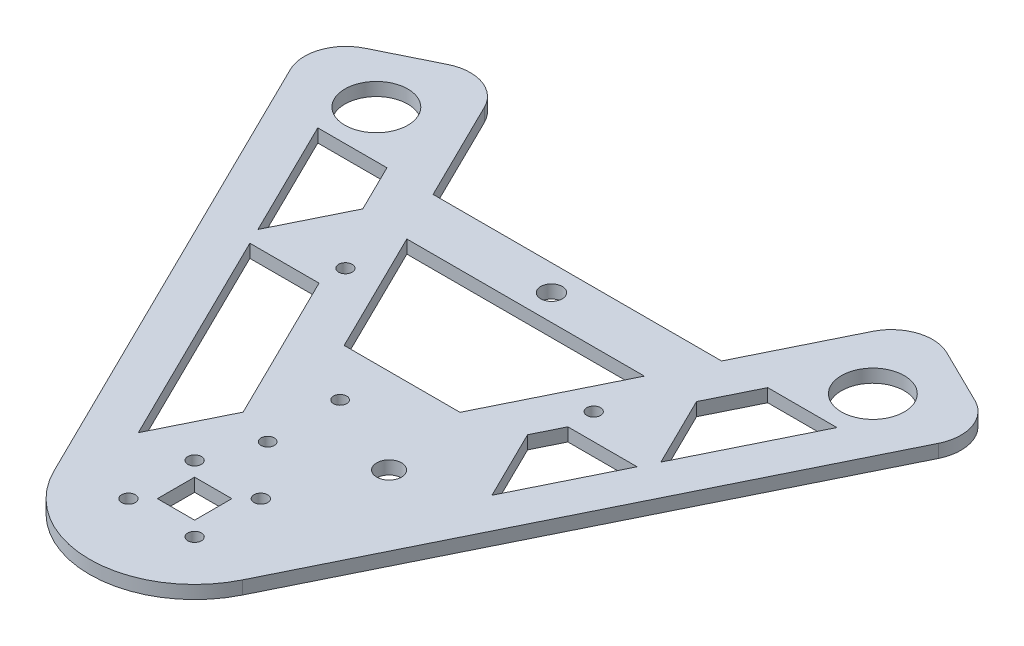
SolidWorks part; units mm, degrees
ref_plane "Front Plane" through (0, 0, 0) normal (0, 0, 1) x (1, 0, 0)
ref_plane "Top Plane" through (0, 0, 0) normal (0, 1, 0) x (1, 0, 0)
ref_plane "Right Plane" through (0, 0, 0) normal (1, 0, 0) x (0, 0, -1)
sketch "Sketch1" plane through (0, 0, 0) normal (0, 1, 0) x (1, 0, 0)
  line L0 (-60, 103.923) -> (60, 103.923) construction
  line L1 (-4.5, -4.5) -> (4.5, -4.5)
  line L2 (-4.5, -4.5) -> (-4.5, 4.5)
  line L3 (-4.5, 4.5) -> (4.5, 4.5)
  line L4 (4.5, -4.5) -> (4.5, 4.5)
  line L5 (-4.5, -4.5) -> (4.5, 4.5) construction
  line L6 (-4.5, 4.5) -> (4.5, -4.5) construction
  line L7 (-82.7138, 110.4306) -> (-22.7854, -11.2243)
  line L8 (22.7854, -11.2243) -> (82.7138, 110.4306)
  line L9 (-51.3166, 125.8972) -> (0, 21.7243)
  line L10 (0, 21.7243) -> (51.3166, 125.8972)
  line L11 (51.3166, 125.8972) -> (82.7138, 110.4306)
  line L12 (-82.7138, 110.4306) -> (-51.3166, 125.8972)
  line L13 (-57.6253, 99.1025) -> (-36.2274, 55.6644) construction
  line L14 (-10.5551, -39.3043) -> (22084.5437, 44813.8629) construction
  line L15 (-14, 50.1443) -> (14, 50.1443)
  line L16 (17.5, 29.5105) -> (-3.1, 29.5105) construction
  line L17 (-8, -8) -> (8, -8) construction
  line L18 (-8, -8) -> (-8, 8) construction
  line L19 (-8, 8) -> (8, 8) construction
  line L20 (8, -8) -> (8, 8) construction
  line L21 (-8, -8) -> (8, 8) construction
  line L22 (-8, 8) -> (8, -8) construction
  line L23 (-3.1, 38.2605) -> (-3.1, 20.7605) construction
  line L24 (-30, 66.4531) -> (30, 66.4531) construction
  line L25 (-34.8648, 92.5) -> (34.8648, 92.5)
  line L26 (-28.7072, 80) -> (28.7072, 80)
  line L27 (0, 80) -> (0, 92.5) construction
  circle A0 centre (60, 103.923) radius 7.6
  circle A1 centre (-60, 103.923) radius 7.6
  arc A2 (22.7854, -11.2243) -> (-22.7854, -11.2243) centre (0, 0) cw
  circle A6 centre (-30, 66.4531) radius 1.65
  circle A7 centre (30, 66.4531) radius 1.65
  circle A8 centre (17.5, 29.5105) radius 3
  circle A9 centre (-8, 8) radius 1.65
  circle A10 centre (8, 8) radius 1.65
  circle A11 centre (8, -8) radius 1.65
  circle A12 centre (-8, -8) radius 1.65
  circle A13 centre (-3.1, 38.2605) radius 1.6
  circle A14 centre (-3.1, 20.7605) radius 1.6
  circle A15 centre (0, 86.25) radius 2.6
  point P4 (0, 0)
  point P10 (0, 103.923)
  point P19 (67.0152, 118.1639)
  point P20 (-67.0152, 118.1639)
  point P45 (0, 66.4531)
  point P49 (-3.1, 29.5105)
  point P56 (0, 86.25)
  dimension "D3" = 15.2
  dimension "D7" = 25.4
  dimension "D8" = 3.3
  dimension "D9" = 48
  dimension "D11" = 6
  dimension "D14" = 3.3
  dimension "D17" = 3.2
  dimension "D22" = 5.2
  dimension "D1" = 9
  dimension "D2" = 35
  dimension "D4" = 120
  dimension "D5" = 120
  dimension "D6" = 15.875
  dimension "D10" = 28
  dimension "D12" = 39
  dimension "D13" = 16
  dimension "D15" = 20.6
  dimension "D16" = 17.5
  dimension "D18" = 60
  dimension "D19" = 17.5
  dimension "D20" = 12.5
  dimension "D21" = 80
extrude "Boss-Extrude1" add sketch "Sketch1" along normal blind 3.175
fillet "Fillet1" radius 10 4 edges at (82.7138, 1.5875, -110.4306) (51.3166, 1.5875, -125.8972) (-51.3166, 1.5875, -125.8972) (-82.7138, 1.5875, -110.4306)
sketch "Sketch2" plane through (0, 3.175, 0) normal (0, 1, 0) x (1, 0, 0)
  line L0 (-46.7948, 60.1443) -> (-30.0736, 60.1443)
  line L1 (-30.0736, 60.1443) -> (-12.2548, 23.9721)
  line L2 (-12.2548, 23.9721) -> (-20.6154, 7)
  line L3 (-20.6154, 7) -> (-46.7948, 60.1443)
  line L8 (-62.7335, 92.5) -> (-48.6941, 64)
  line L9 (-48.6941, 64) -> (-40.3335, 80.9721)
  line L10 (-40.3335, 80.9721) -> (-46.0123, 92.5)
  line L11 (-46.0123, 92.5) -> (-62.7335, 92.5)
  line L12 (-78.2948, 101.46) -> (-22.7854, -11.2243) construction
  line L13 (-33.7051, 33.5722) -> (-42.6757, 29.1532) construction
  line L14 (-55.7138, 78.25) -> (-64.6845, 73.831) construction
  line L15 (-43.1729, 86.736) -> (-34.2023, 91.1551) construction
  line L16 (-21.1642, 42.0582) -> (-12.1935, 46.4772) construction
  line L17 (-28.7072, 80) -> (-14, 50.1443) construction
  line L18 (14, 50.1443) -> (28.7072, 80) construction
  line L19 (-28.7072, 80) -> (28.7072, 80) construction
  line L20 (-34.8648, 92.5) -> (34.8648, 92.5) construction
  line L21 (-14, 50.1443) -> (14, 50.1443) construction
  line L22 (30.0736, 60.1443) -> (46.7948, 60.1443)
  line L23 (46.7948, 60.1443) -> (35.2185, 36.6443)
  line L24 (35.2185, 36.6443) -> (26.8579, 53.6164)
  line L25 (26.8579, 53.6164) -> (30.0736, 60.1443)
  line L26 (46.0123, 92.5) -> (62.7335, 92.5)
  line L27 (62.7335, 92.5) -> (48.6941, 64)
  line L28 (48.6941, 64) -> (40.3335, 80.9721)
  line L29 (40.3335, 80.9721) -> (46.0123, 92.5)
  line L30 (22.7854, -11.2243) -> (78.2948, 101.46) construction
  line L31 (55.7138, 78.25) -> (64.6845, 73.831) construction
  line L32 (43.1729, 86.736) -> (34.2023, 91.1551) construction
  line L33 (34.8648, 92.5) -> (46.8976, 116.9266) construction
  dimension "D1" = 10
  dimension "D2" = 10
  dimension "D3" = 16
  dimension "D4" = 7
  dimension "D5" = 13.5
extrude "Cut-Extrude1" cut sketch "Sketch2" against normal through all both and the other way through all
